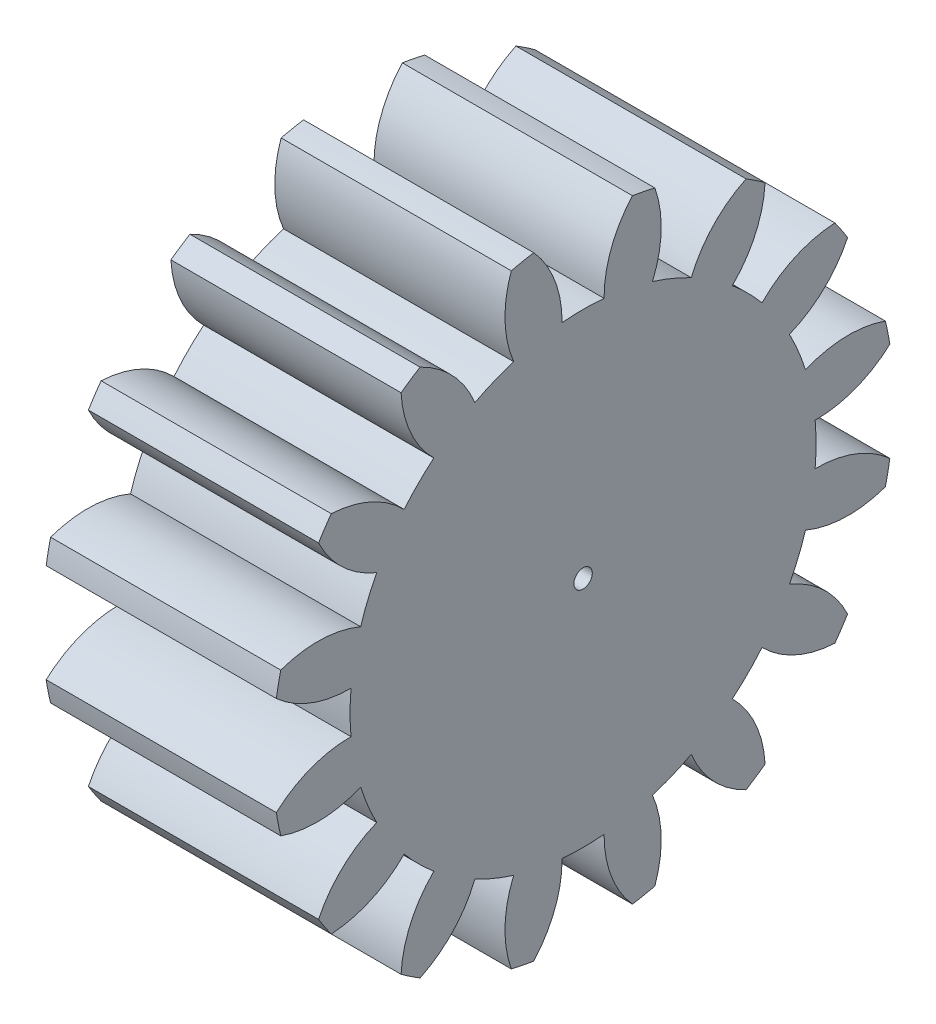
SolidWorks part; units mm, degrees
ref_plane "Plane1" through (0, 0, 0) normal (0, 0, 1) x (1, 0, 0)
ref_plane "Plane2" through (0, 0, 0) normal (0, 1, 0) x (1, 0, 0)
ref_plane "Plane3" through (0, 0, 0) normal (1, 0, 0) x (0, 0, -1)
sketch "HoldingSke" plane through (0, 0, 0) normal (0, 1, 0) x (1, 0, 0)
  line L0 (0, 0) -> (0.6408, -0.1838)
  line L1 (-15, 0) -> (100, 0) construction
  line L2 (0, 0) -> (-2.1039, 2.3779)
  line L3 (0, 0) -> (-11.863, 4.5341)
  line L4 (0, 0) -> (8.3015, 2.3804)
  line L5 (0, 0) -> (-46.8476, -17.4728)
  line L6 (0, 0) -> (-8.2896, -5.593)
  line L7 (-2.1039, 2.3779) -> (8.6586, 51.2059)
  line L8 (-76.2, 54.61) -> (-76.1, 54.61)
  line L9 (-67.7845, 28.3722) -> (-49.3413, 33.142)
  line L10 (-76.2, 71.12) -> (104.1128, 71.12)
  line L11 (0, 0) -> (-10, 0)
  line L12 (-76.2, 101.6) -> (-76.147, 101.6)
  line L13 (24.9733, 27.94) -> (52.9518, 28.4284)
  line L14 (24.9733, 27.94) -> (24.9743, 27.94)
  line L15 (24.9733, 27.94) -> (100.4006, 29.5858)
  line L16 (-63.627, -1.5) -> (-12.827, -1.5)
  circle A0 centre (0, 0) radius 0.4
  circle A1 centre (0, 0) radius 10.124
  circle A2 centre (0, 0) radius 37.5
  circle A3 centre (0, 0) radius 0.4
  dimension "MHD" = 20.248
  dimension "Hub_dia" = 75
  dimension "Bore" = 0.8
  dimension "MBD" = 0.8
  dimension "Num_teeth" = 16
  dimension "Pitch" = 0.6667
  dimension "Overall_len" = 50
  dimension "Show_teeth" = 16
  dimension "Thickness" = 10
  dimension "OAL" = 50.0001
  dimension "T_dim" = 0.1
  dimension "Ap" = 14.5
  dimension "H" = 19.05
  dimension "Pitch_radius" = 180.3128
  dimension "Width" = 10
  dimension "Backlash" = 0.053
  dimension "Addendum_fac" = 1
  dimension "Dedendum_fac" = 1.25
  dimension "Clearance_fac" = 0.25
  dimension "Dedendum_add" = 0.001
  dimension "Module" = 1.5
sketch "BasProSke" plane through (0, 0, 0) normal (0, 1, 0) x (1, 0, 0)
  line L0 (-10, 0) -> (60, 0) construction
  line L1 (0, 0) -> (0, 13.5)
  line L2 (0, 0) -> (10, 0)
  line L3 (10, 0) -> (10, 13.5)
  line L4 (10, 13.5) -> (0, 13.5)
  dimension "Thickness" = 10
  dimension "Diameter" = 27
revolve "Base-Revolve" add sketch "BasProSke" angle 360 about L0
sketch "TooCutSke" plane through (0, 0, 0) normal (1, 0, 0) x (0, 0, -1)
  line L1 (0, 0) -> (0, 107) construction
  line L2 (0, 0) -> (-1.2689, 11.9327) construction
  line L3 (0, 0) -> (-4.663, 23.4427) construction
  line L4 (-1.2689, 11.9327) -> (-2.3315, 11.7214) construction
  arc A0 (0.9122, 10.0828) -> (-0.9122, 10.0828) centre (0, 0) ccw
  arc A1 (2.1654, 13.3509) -> (-2.1654, 13.3509) centre (0, 0) ccw
  circle A2 centre (0, 0) radius 12 construction
  circle A3 centre (0, 0) radius 11.6178 construction
  arc A4 (-0.9122, 10.0828) -> (-2.1654, 13.3509) centre (-5.712, 10.1166) ccw
  arc A5 (2.1654, 13.3509) -> (0.9122, 10.0828) centre (5.712, 10.1166) ccw
  dimension "Root_dia" = 20.248
  dimension "Overcut_dia" = 27.0508
  dimension "Pitch_dia" = 24
  dimension "Base_dia" = 23.2355
  dimension "Flank_rad" = 4.8
  dimension "Half_ang" = 11.25
  dimension "Half_CT" = 1.0835
extrude "ToothCut" cut sketch "TooCutSke" along normal through all
fillet "Breaks" [suppressed] radius 0.03
fillet "RootFillets" [suppressed] radius 0.376
pattern_circular "TeethCuts" count 16 every 22.5 about axis through (-10, 0, 0) along (1, 0, 0) of "ToothCut", "RootFillets", "Breaks"
sketch "HubNeaOneSke" plane through (0, 0, 0) normal (-1, 0, 0) x (0, 0, 1)
  circle A0 centre (0, 0) radius 10.124
  dimension "Diameter" = 20.248
extrude "HubNearOne" [suppressed] add sketch "HubNeaOneSke" along normal blind 40.0001
sketch "HubNeaBotSke" plane through (0, 0, 0) normal (-1, 0, 0) x (0, 0, 1)
  circle A0 centre (0, 0) radius 10.124
  dimension "Diameter" = 20.248
extrude "HubNearBoth" [suppressed] add sketch "HubNeaBotSke" along normal blind 20
ref_plane "FarPln" through (10, 0, 0) normal (1, 0, 0) x (0, 0, -1)
sketch "HubFarSke" plane through (10, 0, 0) normal (1, 0, 0) x (0, 0, -1)
  circle A0 centre (0, 0) radius 10.124
  dimension "Diameter" = 20.248
extrude "HubFar" [suppressed] add sketch "HubFarSke" along normal blind 20
sketch "BorSke" plane through (0, 0, 0) normal (1, 0, 0) x (0, 0, -1)
  circle A0 centre (0, 0) radius 0.4
  dimension "Diameter" = 0.8
extrude "Bore" cut sketch "BorSke" along normal mid plane 100.0001
sketch "KeySke" plane through (0, 0, 0) normal (1, 0, 0) x (0, 0, -1)
  line L0 (-0.05, 0) -> (-0.05, 0.5)
  line L1 (-0.05, 0.5) -> (0.05, 0.5)
  line L2 (0.05, 0.5) -> (0.05, 0)
  line L3 (0, 0) -> (0, 34) construction
  line L4 (-0.05, 0) -> (0.05, 0)
  dimension "Offset" = 0.5
  dimension "Width" = 0.1
extrude "Keyway" [suppressed] cut sketch "KeySke" along normal mid plane 100.0001
pattern_circular "Keyway2" [suppressed] count 2 every 90 about axis through (-10, 0, 0) along (1, 0, 0)
equation "' \"Module@HoldingSke\" = 6.35"
equation "' \"Num_teeth@HoldingSke\" = 12"
equation "' \"Ap@HoldingSke\" =  20"
equation "' \"Ap@HoldingSke\" = 20"
equation "' \"Width@HoldingSke\" = 0.5 * 25.4"
equation "' \"Hub_dia@HoldingSke\"= 1 * 25.4"
equation "' \"Hub_dia@HoldingSke\" = 1 * 25.4"
equation "' \"Overall_len@HoldingSke\" = 1.0 * 25.4"
equation "' \"Bore@HoldingSke\" = 0.75 * 25.4"
equation "' \"T_dim@HoldingSke\" = 0.1 * 25.4"
equation "' \"Width@KeySke\" = 0.25 * 25.4"
equation "' \"Show_teeth@HoldingSke\" = 13"
equation "' \"Backlash@HoldingSke\" = 0.009 * 25.4"
equation "' \"Addendum_fac@HoldingSke\" = 1.0"
equation "' \"Dedendum_fac@HoldingSke\" = 1.25"
equation "' \"Dedendum_add@HoldingSke\" = 0.00005 * 25.4"
equation "' \"Clearance_fac@HoldingSke\" = 0.25"
equation "\"Pitch@HoldingSke\" = 1 / \"Module@HoldingSke\""
equation "\"Overcut_dia@TooCutSke\" = (\"Num_teeth@HoldingSke\" + 2 * \"Addendum_fac@HoldingSke\") / \"Pitch@HoldingSke\" + 0.002 * 25.4"
equation "\"Pitch_dia@TooCutSke\" = \"Num_teeth@HoldingSke\" / \"Pitch@HoldingSke\""
equation "\"Base_dia@TooCutSke\" = \"Num_teeth@HoldingSke\" / \"Pitch@HoldingSke\" * cos((\"Ap@HoldingSke\"  * 3.14159265 / 180))"
equation "\"Root_dia@TooCutSke\" = (\"Num_teeth@HoldingSke\" + 2) / \"Pitch@HoldingSke\" - 2 * (\"Addendum_fac@HoldingSke\" + \"Dedendum_fac@HoldingSke\") / \"Pitch@HoldingSke\" - \"Dedendum_add@HoldingSke\" * 2"
equation "\"Half_ang@TooCutSke\" = 180 / \"Num_teeth@HoldingSke\""
equation "\"Half_CT@TooCutSke\" = \"Num_teeth@HoldingSke\" / \"Pitch@HoldingSke\" * sin((3.14159265 / 2 / \"Num_teeth@HoldingSke\")) / 2 - 7 * \"Backlash@HoldingSke\" / 4"
equation "\"Flank_rad@TooCutSke\" = \"Num_teeth@HoldingSke\" / \"Pitch@HoldingSke\" / 5"
equation "\"Radius@RootFillets\" = \"Clearance_fac@HoldingSke\" / \"Pitch@HoldingSke\" + \"Dedendum_add@HoldingSke\""
equation "\"Break_rad@Breaks\" = 0.02 / \"Pitch@HoldingSke\""
equation "\"Thickness@HoldingSke\" = \"Width@HoldingSke\""
equation "\"OAL@HoldingSke\" = \"Thickness@HoldingSke\""
equation "\"MHD@HoldingSke\" = (\"Num_teeth@HoldingSke\" + 2) / \"Pitch@HoldingSke\" - 2 * (\"Addendum_fac@HoldingSke\" + \"Dedendum_fac@HoldingSke\")  / \"Pitch@HoldingSke\" - \"Dedendum_add@HoldingSke\" * 2"
equation "\"MBD@HoldingSke\" = (\"Num_teeth@HoldingSke\" + 2) / \"Pitch@HoldingSke\" - 2 * (\"Addendum_fac@HoldingSke\" + \"Dedendum_fac@HoldingSke\")  / \"Pitch@HoldingSke\" - \"Dedendum_add@HoldingSke\" * 2 - 0.002 * 25.4"
equation "\"MHD@HoldingSke\" = ((sgn( \"MHD@HoldingSke\" - \"Hub_dia@HoldingSke\" )-1)*( \"MHD@HoldingSke\" - \"Hub_dia@HoldingSke\" ))/-2+ \"Hub_dia@HoldingSke\""
equation "\"MBD@HoldingSke\" = ((sgn( \"MBD@HoldingSke\" - \"Bore@HoldingSke\" )-1)*( \"MBD@HoldingSke\" - \"Bore@HoldingSke\" ))/-2+ \"Bore@HoldingSke\""
equation "\"OAL@HoldingSke\" = ((sgn( \"OAL@HoldingSke\" - \"Overall_len@HoldingSke\" )+1)*( \"OAL@HoldingSke\" - \"Overall_len@HoldingSke\" ))/2 + \"Overall_len@HoldingSke\" + 0.000002 * 25.4"
equation "\"Num_teeth@TeethCuts\" = int( \"Show_teeth@HoldingSke\" ) + 1"
equation "\"Num_teeth@TeethCuts\" = ((sgn( \"Num_teeth@TeethCuts\" - \"Num_teeth@HoldingSke\" )-1)*( \"Num_teeth@TeethCuts\" - \"Num_teeth@HoldingSke\" ))/-2+ \"Num_teeth@HoldingSke\""
equation "\"Num_teeth@TeethCuts\" = ((sgn( \"Num_teeth@TeethCuts\" - 2.0)+1)*( \"Num_teeth@TeethCuts\" - 2.0))/2 +2.0"
equation "\"Angle@TeethCuts\" = 360.0 / \"Num_teeth@HoldingSke\""
equation "\"Diameter@BasProSke\" = (\"Num_teeth@HoldingSke\" + 2 * \"Addendum_fac@HoldingSke\") / \"Pitch@HoldingSke\""
equation "\"Thickness@BasProSke\"  = \"Thickness@HoldingSke\""
equation "' \"Fillet_rad@BasProSke\" =  \"Thickness@HoldingSke\" * 0.05"
equation "' \"Fillet_rad@BasProSke\" = \"Thickness@HoldingSke\" * 0.05"
equation "\"MHD@HoldingSke\" = ((sgn( \"MHD@HoldingSke\" - \"Root_dia@TooCutSke\" )-1)*( \"MHD@HoldingSke\" - \"Root_dia@TooCutSke\" ))/-2+ \"Root_dia@TooCutSke\""
equation "\"Diameter@HubNeaOneSke\" = \"MHD@HoldingSke\""
equation "\"Length@HubNearOne\" = \"OAL@HoldingSke\" - \"Thickness@BasProSke\""
equation "\"Diameter@HubNeaBotSke\" = \"MHD@HoldingSke\""
equation "\"Length@HubNearBoth\" = ( \"OAL@HoldingSke\" - \"Thickness@BasProSke\" ) / 2.0"
equation "\"Thickness@FarPln\" = \"Thickness@BasProSke\""
equation "\"Diameter@HubFarSke\" = \"MHD@HoldingSke\""
equation "\"Length@HubFar\" = ( \"OAL@HoldingSke\" - \"Thickness@BasProSke\" ) / 2.0"
equation "\"Diameter@BorSke\" = \"MBD@HoldingSke\""
equation "\"D1@Bore\" = \"OAL@HoldingSke\" * 2.0"
equation "\"D1@Keyway\" = \"OAL@HoldingSke\" * 2.0"
equation "\"Offset@KeySke\" = \"T_dim@HoldingSke\" + \"MBD@HoldingSke\" / 2.0"
